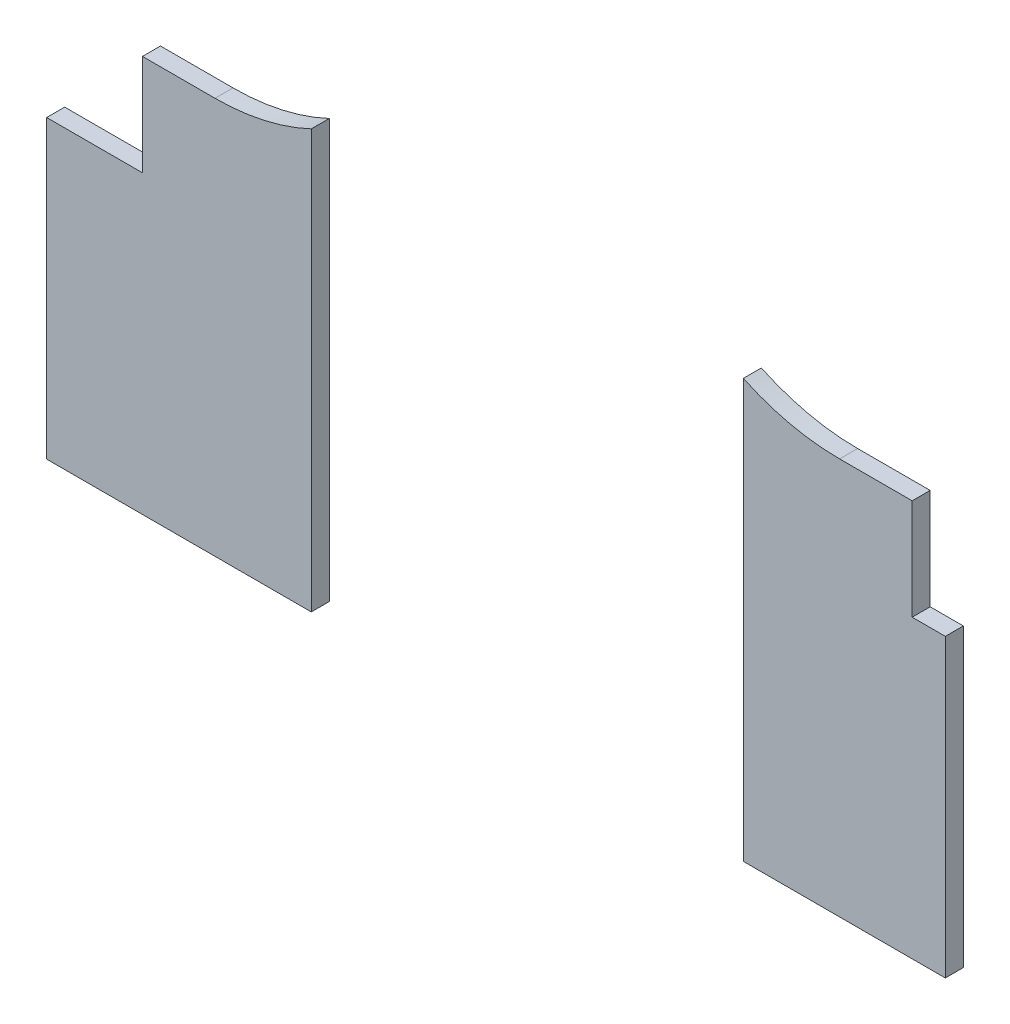
SolidWorks part; units mm, degrees
ref_plane "Front Plane" through (0, 0, 0) normal (0, 0, 1) x (1, 0, 0)
ref_plane "Top Plane" through (0, 0, 0) normal (0, 1, 0) x (1, 0, 0)
ref_plane "Right Plane" through (0, 0, 0) normal (1, 0, 0) x (0, 0, -1)
sketch "Sketch1" plane through (0, 0, 0) normal (0, 0, 1) x (1, 0, 0)
  line L0 (124.8, 0) -> (124.8, -267.4) construction
  line L1 (0, 0) -> (249.6, 0)
  line L2 (0, 0) -> (0, -267.4)
  line L3 (0, -267.4) -> (249.6, -267.4)
  line L4 (249.6, 0) -> (249.6, -267.4)
  line L7 (249.6, -267.4) -> (249.6, -100) construction
  line L8 (249.6, -267.4) -> (0, -267.4) construction
extrude "Boss-Extrude1" add sketch "Sketch1" along normal blind 5
sketch "Sketch5" plane through (0, 0, 5) normal (0, 0, 1) x (1, 0, 0)
  line L4 (0, -195.5612) -> (249.6, -195.5612)
  line L19 (162.0861, 0) -> (249.6, 0)
  line L26 (249.6, 0) -> (0, 0) construction
  line L29 (0, -195.5612) -> (0, -267.4)
  line L30 (0, -267.4) -> (249.6, -267.4)
  line L31 (249.6, -267.4) -> (249.6, -195.5612)
  line L34 (249.6, 0) -> (249.6, -113.3749)
  line L36 (249.6, -267.4) -> (249.6, 0) construction
  line L38 (240.3957, -113.3749) -> (267, -113.3749) construction
  line L39 (249.6, -113.3749) -> (240.3957, -113.3749)
  line L40 (240.3957, -113.3749) -> (240.3957, -85.3749)
  line L41 (240.3957, -85.3749) -> (220.2496, -85.3749)
  line L42 (104.9139, 0) -> (0, 0)
  line L43 (0, 0) -> (0, -113.3749)
  line L44 (0, 0) -> (0, -267.4) construction
  line L45 (0, -113.3749) -> (26.6043, -113.3749) construction
  line L46 (0, -113.3749) -> (26.6043, -113.3749)
  line L47 (26.6043, -113.3749) -> (26.6043, -85.3749)
  line L49 (26.6043, -113.3749) -> (26.6043, -85.3749) construction
  line L50 (26.6043, -85.3749) -> (46.7504, -85.3749)
  arc A5 (220.2496, -85.3749) -> (162.0861, 0) centre (220.2496, -22.8749) cw
  arc A8 (46.7504, -85.3749) -> (109.2504, -22.8749) centre (46.7504, -22.8749) ccw construction
  arc A11 (46.7504, -85.3749) -> (104.9139, 0) centre (46.7504, -22.8749) ccw
  arc A12 (161.9401, -0.3749) -> (220.2496, -85.3749) centre (220.2496, -22.8749) ccw construction
extrude "Cut-Extrude3" cut sketch "Sketch5" against normal through all
sketch "Sketch7" plane through (0, 0, 5) normal (0, 0, 1) x (1, 0, 0)
  line L0 (73.5, -195.5612) -> (193.5, -195.5612)
  line L1 (73.5, -195.5612) -> (73.5, 0)
  line L2 (193.5, -195.5612) -> (193.5, 0)
  line L3 (73.5, 0) -> (193.5, 0)
  line L4 (249.6, -195.5612) -> (0, -195.5612) construction
  line L6 (133.5, 0) -> (133.5, -195.5612) construction
  line L7 (162.0861, 0) -> (104.9139, 0) construction
  point P7 (133.5, 0)
  dimension "D1" = 120
extrude "Cut-Extrude4" cut sketch "Sketch7" against normal through all
